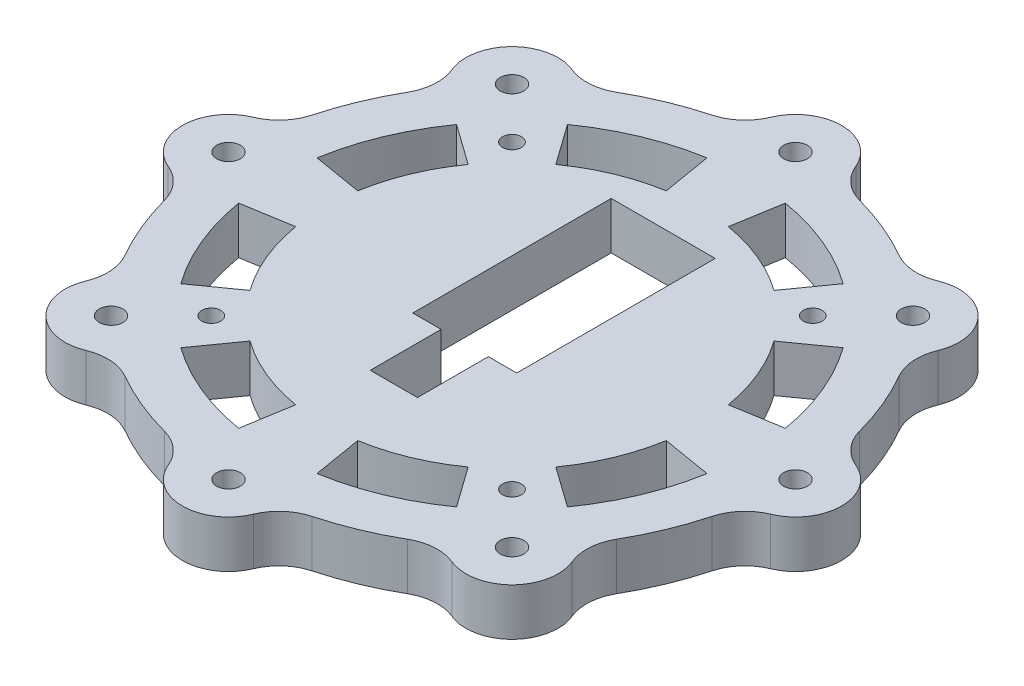
SolidWorks part; units mm, degrees
ref_plane "Alzado" through (0, 0, 0) normal (0, 0, 1) x (1, 0, 0)
ref_plane "Planta" through (0, 0, 0) normal (0, 1, 0) x (1, 0, 0)
ref_plane "Vista lateral" through (0, 0, 0) normal (1, 0, 0) x (0, 0, -1)
sketch "Croquis1" plane through (0, 0, 0) normal (0, 1, 0) x (1, 0, 0)
  line L0 (0, 0) -> (0, 75) construction
  line L1 (0, 0) -> (8.2936, 49.5609)
  line L2 (0, 0) -> (-8.2936, 49.5609)
  line L3 (0, 0) -> (40.9093, 29.1803)
  line L4 (0, 0) -> (29.1803, 40.9093)
  line L5 (0, 0) -> (49.5609, -8.2936)
  line L6 (0, 0) -> (49.5609, 8.2936)
  line L7 (0, 0) -> (29.1803, -40.9093)
  line L8 (0, 0) -> (40.9093, -29.1803)
  line L9 (0, 0) -> (-8.2936, -49.5609)
  line L10 (0, 0) -> (8.2936, -49.5609)
  line L11 (0, 0) -> (-40.9093, -29.1803)
  line L12 (0, 0) -> (-29.1803, -40.9093)
  line L13 (0, 0) -> (-49.5609, 8.2936)
  line L14 (0, 0) -> (-49.5609, -8.2936)
  line L15 (0, 0) -> (-29.1803, 40.9093)
  line L16 (0, 0) -> (-40.9093, 29.1803)
  line L17 (0, 0) -> (0, -82.5226) construction
  line L18 (-11, 32) -> (11, 32)
  line L19 (-11, 32) -> (-11, -10)
  line L20 (-11, -10) -> (11, -10)
  line L21 (11, 32) -> (11, -10)
  line L22 (-11, 32) -> (11, -10) construction
  line L23 (-11, -10) -> (11, 32) construction
  line L24 (0, 0) -> (42.4264, 42.4264) construction
  circle A1 centre (0, 0) radius 50.25
  circle A2 centre (0, 0) radius 39.75
  circle A3 centre (0, -60) radius 2.5
  circle A4 centre (-42.4264, -42.4264) radius 2.5
  circle A5 centre (-60, 0) radius 2.5
  circle A6 centre (-42.4264, 42.4264) radius 2.5
  circle A7 centre (0, 60) radius 2.5
  circle A8 centre (42.4264, 42.4264) radius 2.5
  circle A9 centre (60, 0) radius 2.5
  circle A10 centre (42.4264, -42.4264) radius 2.5
  circle A11 centre (31.8198, 31.8198) radius 2
  circle A12 centre (31.8198, -31.8198) radius 2
  circle A13 centre (-31.8198, -31.8198) radius 2
  circle A14 centre (-31.8198, 31.8198) radius 2
  circle A15 centre (0, 0) radius 60
  circle A16 centre (0, -60) radius 9.75
  circle A17 centre (-42.4264, -42.4264) radius 9.75
  circle A18 centre (-60, 0) radius 9.75
  circle A19 centre (-42.4264, 42.4264) radius 9.75
  circle A20 centre (0, 60) radius 9.75
  circle A21 centre (42.4264, 42.4264) radius 9.75
  circle A22 centre (60, 0) radius 9.75
  circle A23 centre (42.4264, -42.4264) radius 9.75
  point P5 (0, 11)
  point P25 (0, 0)
  point P48 (0, 0)
  point P57 (0, 0)
  point P74 (0, 0)
  dimension "D2" = 100.5
  dimension "D3" = 79.5
  dimension "D10" = 5
  dimension "D14" = 4
  dimension "D17" = 120
  dimension "D18" = 8
  dimension "D4" = 9.5
  dimension "D5" = 9.5
  dimension "D7" = 42
  dimension "D8" = 22
  dimension "D9" = 10
  dimension "D11" = 60
  dimension "D13" = 45
  dimension "D15" = 45
  dimension "D6" = 8
  dimension "D12" = 8
  dimension "D16" = 4
extrude "Saliente-Extruir1" add sketch "Croquis1" along normal blind 10
fillet "Redondeo1" radius 10 16 edges at (34.9947, 5, -48.7377) (48.7377, 5, -34.9947) (59.2078, 5, -9.7178) (59.2078, 5, 9.7178) (48.7377, 5, 34.9947) (34.9947, 5, 48.7377) (9.7178, 5, 59.2078) (-9.7178, 5, 59.2078) (-34.9947, 5, 48.7377) (-48.7377, 5, 34.9947) (-59.2078, 5, 9.7178) (-59.2078, 5, -9.7178) (-48.7377, 5, -34.9947) (-34.9947, 5, -48.7377) (-9.7178, 5, -59.2078) (9.7178, 5, -59.2078)
sketch "Croquis2" plane through (0, 0, 0) normal (0, -1, 0) x (1, 0, 0)
  circle A0 centre (31.8198, 31.8198) radius 5
  circle A1 centre (31.8198, -31.8198) radius 5
  circle A2 centre (-31.8198, -31.8198) radius 5
  circle A3 centre (-31.8198, 31.8198) radius 5
  point P13 (0, 0)
  dimension "D1" = 10
  dimension "D2" = 4
extrude "Cortar-Extruir1" cut sketch "Croquis2" against normal blind 5
sketch "Croquis3" plane through (0, 10, 0) normal (0, 1, 0) x (1, 0, 0)
  line L0 (-11, -10) -> (11, -10) construction
  line L1 (-5, -10) -> (5, -10)
  line L2 (-5, -10) -> (-5, -25)
  line L3 (-5, -25) -> (5, -25)
  line L4 (5, -10) -> (5, -25)
  point P6 (5, -17.5)
  dimension "D1" = 5
  dimension "D2" = 5
  dimension "D3" = 15
extrude "Cortar-Extruir2" cut sketch "Croquis3" against normal blind 10
